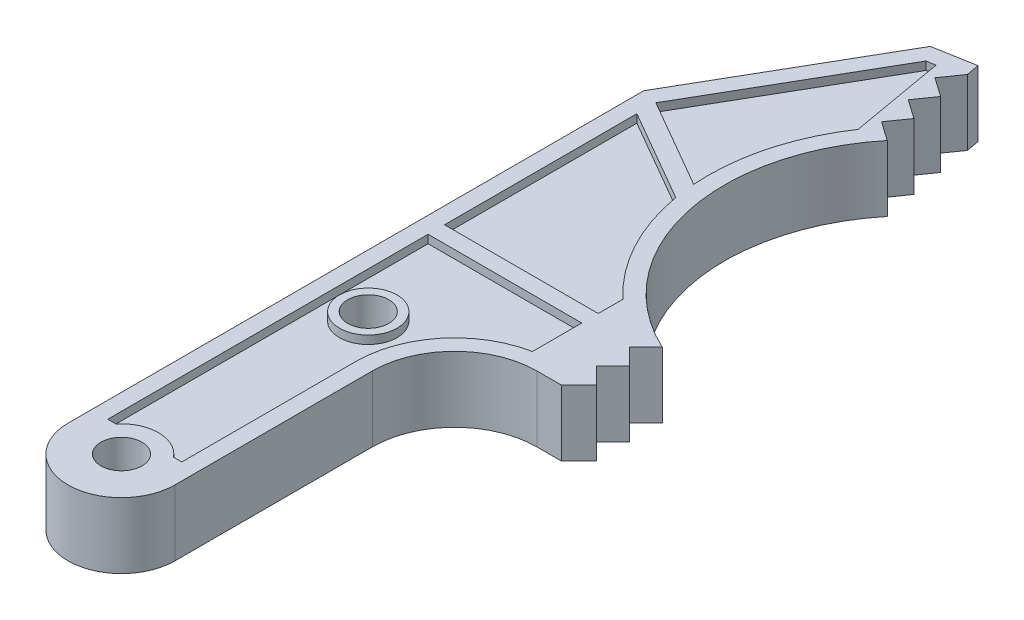
SolidWorks part; units mm, degrees
ref_plane "Alzado" through (0, 0, 0) normal (0, 0, 1) x (1, 0, 0)
ref_plane "Planta" through (0, 0, 0) normal (0, 1, 0) x (1, 0, 0)
ref_plane "Vista lateral" through (0, 0, 0) normal (1, 0, 0) x (0, 0, -1)
sketch "Croquis2" plane through (0, 0, 0) normal (0, 1, 0) x (1, 0, 0)
  line L0 (11.4519, 91.3762) -> (12.1465, 87.437) construction
  line L1 (9.8296, 89.0593) -> (11.7992, 89.4066) construction
  line L2 (12.1465, 87.437) -> (12.8411, 83.4977) construction
  line L3 (10.5241, 85.1201) -> (12.4938, 85.4673) construction
  line L4 (12.8411, 83.4977) -> (13.5357, 79.5585) construction
  line L5 (13.1884, 81.5281) -> (11.2187, 81.1808) construction
  line L6 (21.6213, 44.1213) -> (21.6213, 40.1213) construction
  line L7 (21.6213, 42.1213) -> (19.6213, 42.1213) construction
  line L8 (21.6213, 40.1213) -> (21.6213, 36.1213) construction
  line L9 (21.6213, 38.1213) -> (19.6213, 38.1213) construction
  line L36 (-6.5, 70) -> (-6.5, 0)
  line L37 (6.5, 0) -> (6.5, 24)
  line L38 (16.5, 34) -> (19.5, 34)
  line L39 (19.5, 34) -> (21.6213, 36.1213)
  line L40 (21.6213, 36.1213) -> (19.6213, 38.1213)
  line L41 (19.6213, 38.1213) -> (21.6213, 40.1213)
  line L42 (21.6213, 40.1213) -> (19.6213, 42.1213)
  line L43 (19.6213, 42.1213) -> (21.6213, 44.1213)
  line L45 (13.5357, 79.5585) -> (11.2187, 81.1808)
  line L46 (11.2187, 81.1808) -> (12.8411, 83.4977)
  line L47 (12.8411, 83.4977) -> (10.5241, 85.1201)
  line L48 (10.5241, 85.1201) -> (12.1465, 87.437)
  line L49 (12.1465, 87.437) -> (9.8296, 89.0593)
  line L50 (9.8296, 89.0593) -> (11.4519, 91.3762)
  line L51 (11.4519, 91.3762) -> (11.174, 92.9519)
  line L52 (11.174, 92.9519) -> (6.25, 92.0836)
  line L53 (6.25, 92.0836) -> (-6.5, 70)
  circle A0 centre (0, 0) radius 2.5
  circle A1 centre (0, 30) radius 2.5
  arc A11 (-6.5, 0) -> (6.5, 0) centre (0, 0) ccw
  arc A12 (16.5, 34) -> (6.5, 24) centre (16.5, 24) ccw
  arc A13 (13.5357, 79.5585) -> (21.6213, 44.1213) centre (31.3216, 64.9757) ccw
  dimension "D1" = 6.5
  dimension "D2" = 10
  dimension "D5" = 25.5
  dimension "D11" = 23
  dimension "D13" = 5
  dimension "D3" = 24
  dimension "D4" = 70
  dimension "D6" = 150
  dimension "D7" = 130
  dimension "D8" = 5
  dimension "D9" = 90
  dimension "D10" = 1.6
  dimension "D12" = 4
  dimension "D14" = 3
  dimension "D15" = 3
  dimension "D16" = 30
extrude "Saliente-Extruir1" add sketch "Croquis2" along normal blind 8
sketch "Croquis3" plane through (0, 8, 0) normal (0, 1, 0) x (1, 0, 0)
  line L0 (7.5157, 90.276) -> (-4.5, 69.4641)
  line L1 (-4.5, 67.1547) -> (-4.5, 43.7743)
  line L2 (-4.5, 43.7743) -> (14.1836, 43.7743)
  line L3 (8.5669, 90.4613) -> (10.5957, 78.9555)
  line L4 (-4.5, 69.4641) -> (6.3863, 63.1789)
  line L5 (-4.5, 67.1547) -> (6.6911, 60.6935)
  line L7 (-4.5, 69.4641) -> (10.5957, 60.7486) construction
  line L8 (-5.5, 67.7321) -> (9.5957, 59.0165) construction
  line L55 (6.25, 92.0836) -> (-6.5, 70) construction
  line L56 (11.4519, 91.3762) -> (11.174, 92.9519) construction
  line L57 (7.5157, 90.276) -> (8.5669, 90.4613)
  line L58 (11.174, 92.9519) -> (6.25, 92.0836) construction
  line L59 (11.4519, 91.3762) -> (11.174, 92.9519) construction
  line L60 (-6.5, 70) -> (-6.5, 0) construction
  line L71 (-4.5, 2.8284) -> (-4.5, 41.7743)
  line L72 (-4.5, 41.7743) -> (14.1836, 41.7743)
  line L73 (14.1836, 41.7743) -> (14.1836, 35.7743)
  line L75 (14.1836, 43.7743) -> (14.1836, 46.7743)
  line L76 (4.5, 0) -> (4.5, 24)
  line L77 (4.5, 2.8284) -> (4.5, 24)
  line L78 (-4.5, 2.8284) -> (-3.5, 2.8284)
  line L79 (3.5, 2.8284) -> (4.5, 2.8284)
  arc A1 (6.6911, 60.6935) -> (14.1836, 46.7743) centre (31.3216, 64.9757) ccw
  circle A2 centre (0, 30) radius 3.5
  circle A3 centre (0, 30) radius 3.5
  arc A11 (11.989, 80.8266) -> (20.7778, 42.3079) centre (31.3216, 64.9757) ccw
  arc A12 (10.5957, 78.9555) -> (6.3863, 63.1789) centre (31.3216, 64.9757) ccw
  circle A22 centre (0, 0) radius 4.5
  arc A23 (3.5, 2.8284) -> (-3.5, 2.8284) centre (0, 0) ccw
  arc A26 (16.5, 36) -> (4.5, 24) centre (16.5, 24) ccw
  arc A27 (14.1836, 35.7743) -> (4.5, 24) centre (16.5, 24) ccw
  point P0 (11.313, 92.164)
  dimension "D2" = 2
  dimension "D3" = 2
  dimension "D4" = 3
  dimension "D5" = 2
  dimension "D8" = 2
  dimension "D9" = 6
  dimension "D10" = 3
  dimension "D11" = 1
  dimension "D14" = 23.3804
  dimension "D1" = 2
  dimension "D6" = 2
  dimension "D7" = 2
  dimension "D12" = 1
  dimension "D13" = 2
extrude "Cortar-Extruir1" cut sketch "Croquis3" against normal blind 1
sketch "Croquis4" plane through (0, 0, 0) normal (0, -1, 0) x (1, 0, 0)
  line L4 (6.3863, -63.1789) -> (-4.5, -69.4641)
  line L5 (-4.5, -69.4641) -> (7.5157, -90.276)
  line L6 (4.5, -24) -> (4.5, -2.8284)
  line L7 (14.1836, -41.7743) -> (14.1836, -35.7743)
  line L8 (-4.5, -41.7743) -> (14.1836, -41.7743)
  line L9 (-4.5, -2.8284) -> (-4.5, -41.7743)
  line L10 (-3.5, -2.8284) -> (-4.5, -2.8284)
  line L11 (4.5, -2.8284) -> (3.5, -2.8284)
  line L12 (4.5, -24) -> (4.5, -2.8284)
  line L13 (14.1836, -41.7743) -> (14.1836, -35.7743)
  line L14 (-4.5, -41.7743) -> (14.1836, -41.7743)
  line L15 (-4.5, -2.8284) -> (-4.5, -41.7743)
  line L16 (-3.5, -2.8284) -> (-4.5, -2.8284)
  line L17 (4.5, -2.8284) -> (3.5, -2.8284)
  line L18 (7.5157, -90.276) -> (8.5669, -90.4613)
  line L19 (8.5669, -90.4613) -> (10.5957, -78.9555)
  line L20 (6.3863, -63.1789) -> (-4.5, -69.4641)
  line L21 (-4.5, -69.4641) -> (7.5157, -90.276)
  line L22 (7.5157, -90.276) -> (8.5669, -90.4613)
  line L23 (8.5669, -90.4613) -> (10.5957, -78.9555)
  line L24 (-4.5, -67.1547) -> (6.6911, -60.6935)
  line L25 (14.1836, -46.7743) -> (14.1836, -43.7743)
  line L26 (14.1836, -43.7743) -> (-4.5, -43.7743)
  line L27 (-4.5, -43.7743) -> (-4.5, -67.1547)
  line L28 (-4.5, -67.1547) -> (6.6911, -60.6935)
  line L29 (14.1836, -46.7743) -> (14.1836, -43.7743)
  line L30 (14.1836, -43.7743) -> (-4.5, -43.7743)
  line L31 (-4.5, -43.7743) -> (-4.5, -67.1547)
  circle A2 centre (0, -30) radius 3.5
  circle A3 centre (0, -30) radius 3.5
  arc A4 (6.3863, -63.1789) -> (10.5957, -78.9555) centre (31.3216, -64.9757) ccw
  arc A5 (4.5, -24) -> (14.1836, -35.7743) centre (16.5, -24) ccw
  arc A6 (-3.5, -2.8284) -> (3.5, -2.8284) centre (0, 0) ccw
  arc A7 (4.5, -24) -> (14.1836, -35.7743) centre (16.5, -24) ccw
  arc A8 (-3.5, -2.8284) -> (3.5, -2.8284) centre (0, 0) ccw
  arc A9 (6.3863, -63.1789) -> (10.5957, -78.9555) centre (31.3216, -64.9757) ccw
  arc A10 (14.1836, -46.7743) -> (6.6911, -60.6935) centre (31.3216, -64.9757) ccw
  arc A11 (14.1836, -46.7743) -> (6.6911, -60.6935) centre (31.3216, -64.9757) ccw
  dimension "D1" = 0
  dimension "D2" = 0
  dimension "D3" = 0
  dimension "D4" = 0
extrude "Cortar-Extruir2" cut sketch "Croquis4" against normal blind 1
